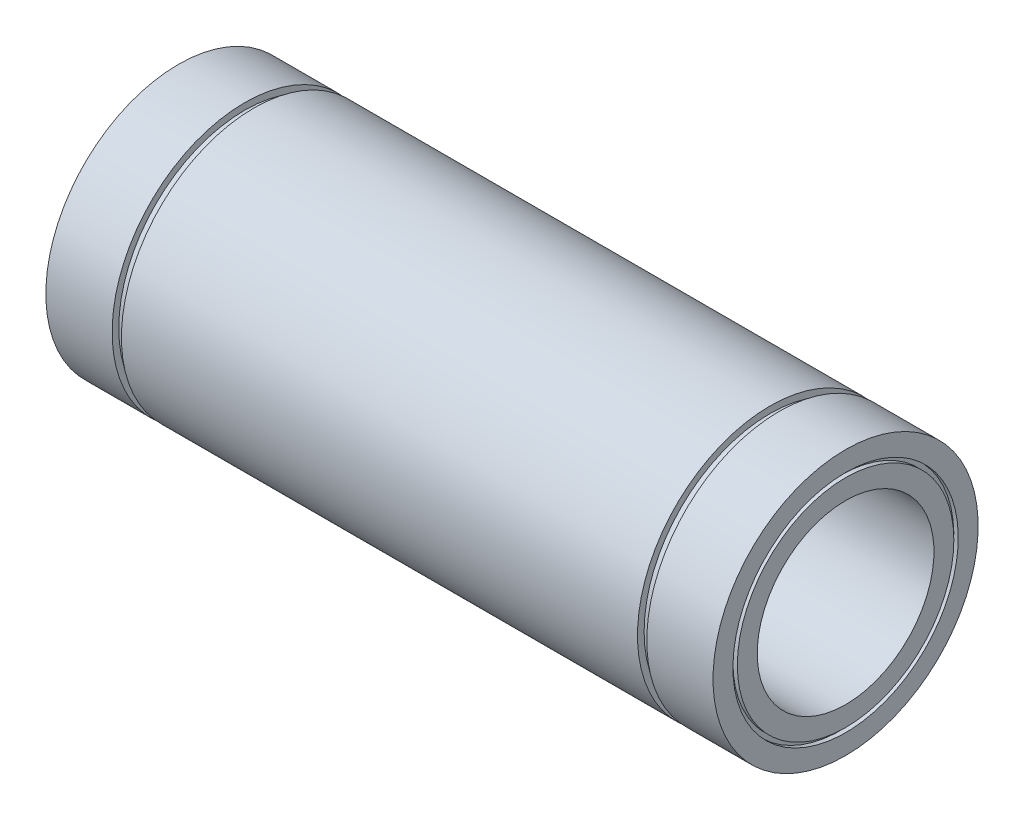
SolidWorks part; units mm, degrees
material "Ст3сп ГОСТ 535-2005"
ref_plane "Plano frontal" through (0, 0, 0) normal (0, 0, 1) x (1, 0, 0)
ref_plane "Plano superior" through (0, 0, 0) normal (0, 1, 0) x (1, 0, 0)
ref_plane "Plano direito" through (0, 0, 0) normal (1, 0, 0) x (0, 0, -1)
sketch "Esboço1" plane through (0, 0, 0) normal (0, 0, 1) x (1, 0, 0)
  line L0 (-75.5, 30) -> (-60.5, 30)
  line L1 (-60.5, 30) -> (-60.5, 28.5)
  line L2 (-60.5, 28.5) -> (-58.4, 28.5)
  line L3 (-58.4, 28.5) -> (-58.4, 30)
  line L4 (-58.4, 30) -> (58.4, 30)
  line L5 (58.4, 30) -> (58.4, 28.5)
  line L6 (58.4, 28.5) -> (60.5, 28.5)
  line L7 (60.5, 28.5) -> (60.5, 30)
  line L8 (60.5, 30) -> (75.5, 30)
  line L9 (75.5, 30) -> (75.5, 25.5)
  line L10 (75.5, 20) -> (-75.5, 20)
  line L11 (-75.5, 20) -> (-75.5, 24.5)
  line L12 (0, 20) -> (0, 0) construction
  line L13 (0, 0) -> (-86.5, 0) construction
  line L14 (-75.5, 25.5) -> (-75.5, 30)
  line L15 (-75.5, 25.5) -> (-74.5, 25.5)
  line L16 (75.5, 24.5) -> (75.5, 20)
  line L17 (-74.5, 25.5) -> (-74.5, 24.5)
  line L18 (-74.5, 24.5) -> (-75.5, 24.5)
  line L19 (75.5, 25.5) -> (74.5, 25.5)
  line L21 (75.5, 24.5) -> (74.5, 24.5)
  line L22 (74.5, 25.5) -> (74.5, 24.5)
  dimension "D1" = 151
  dimension "D2" = 121
  dimension "D3" = 2.1
  dimension "D4" = 40
  dimension "D5" = 60
  dimension "D6" = 57
  dimension "D7" = 1
  dimension "D8" = 1
  dimension "D9" = 1
  dimension "D10" = 1
revolve "Revolução1" add sketch "Esboço1" angle 360 about L13
